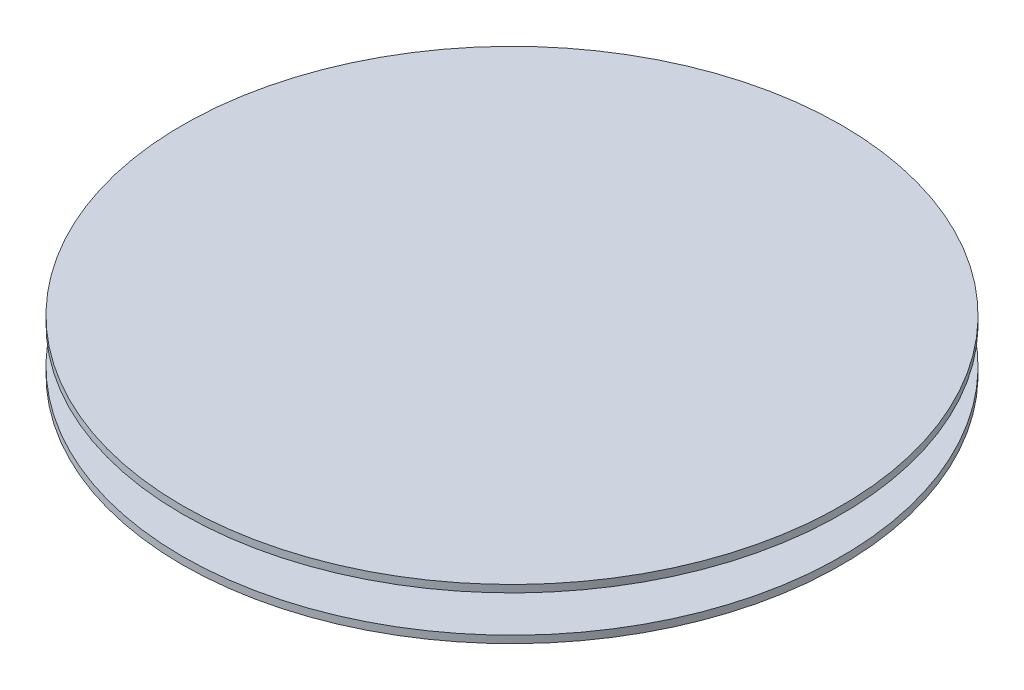
SolidWorks part; units mm, degrees
ref_plane "Front Plane" through (0, 0, 0) normal (0, 0, 1) x (1, 0, 0)
ref_plane "Top Plane" through (0, 0, 0) normal (0, 1, 0) x (1, 0, 0)
ref_plane "Right Plane" through (0, 0, 0) normal (1, 0, 0) x (0, 0, -1)
sketch "Sketch1" plane through (0, 0, 0) normal (0, 1, 0) x (1, 0, 0)
  circle A0 centre (0, 0) radius 90
  circle A1 centre (0, 0) radius 75
extrude "Boss-Extrude1" add sketch "Sketch1" along normal blind 2
sketch "Sketch2" plane through (0, 2, 0) normal (0, 1, 0) x (1, 0, 0)
  circle A0 centre (0, 0) radius 75
extrude "Boss-Extrude2" add sketch "Sketch2" along normal blind 10 separate body contours A0
ref_plane "Plane1" through (0, 12, 0) normal (0, 1, 0) x (1, 0, 0)
sketch "Sketch4" plane through (0, 12, 0) normal (0, 1, 0) x (1, 0, 0)
  circle A0 centre (0, 0) radius 90
extrude "Boss-Extrude3" add sketch "Sketch4" along normal blind 2
sketch "Sketch5" plane through (0, 2, 0) normal (0, -1, 0) x (1, 0, 0)
  circle A0 centre (0, 0) radius 70
extrude "Cut-Extrude2" cut sketch "Sketch5" against normal blind 8 contours A0
